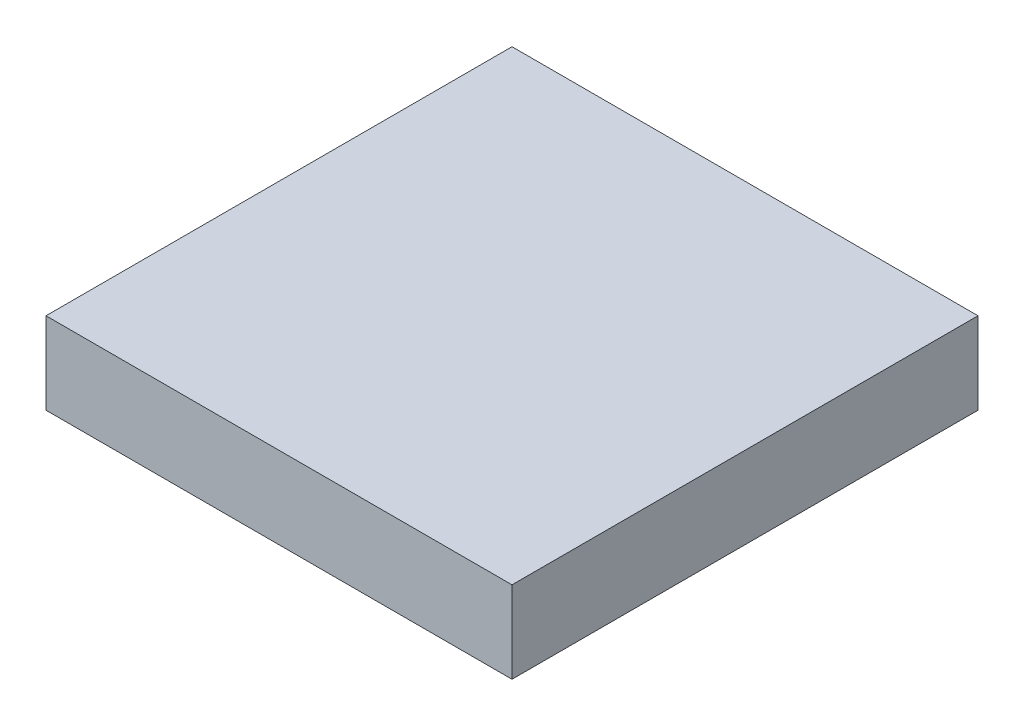
SolidWorks part; units mm, degrees
ref_plane "Front Plane" through (0, 0, 0) normal (0, 0, 1) x (1, 0, 0)
ref_plane "Top Plane" through (0, 0, 0) normal (0, 1, 0) x (1, 0, 0)
ref_plane "Right Plane" through (0, 0, 0) normal (1, 0, 0) x (0, 0, -1)
sketch "Sketch1" plane through (0, 0, 0) normal (0, 1, 0) x (1, 0, 0)
  line L1 (0, 0) -> (25.4, 0)
  line L2 (0, 0) -> (0, -25.4)
  line L3 (0, -25.4) -> (25.4, -25.4)
  line L4 (25.4, 0) -> (25.4, -25.4)
  dimension "D1" = 25.4
  dimension "D2" = 25.4
extrude "Boss-Extrude1" add sketch "Sketch1" along normal blind 4.46
